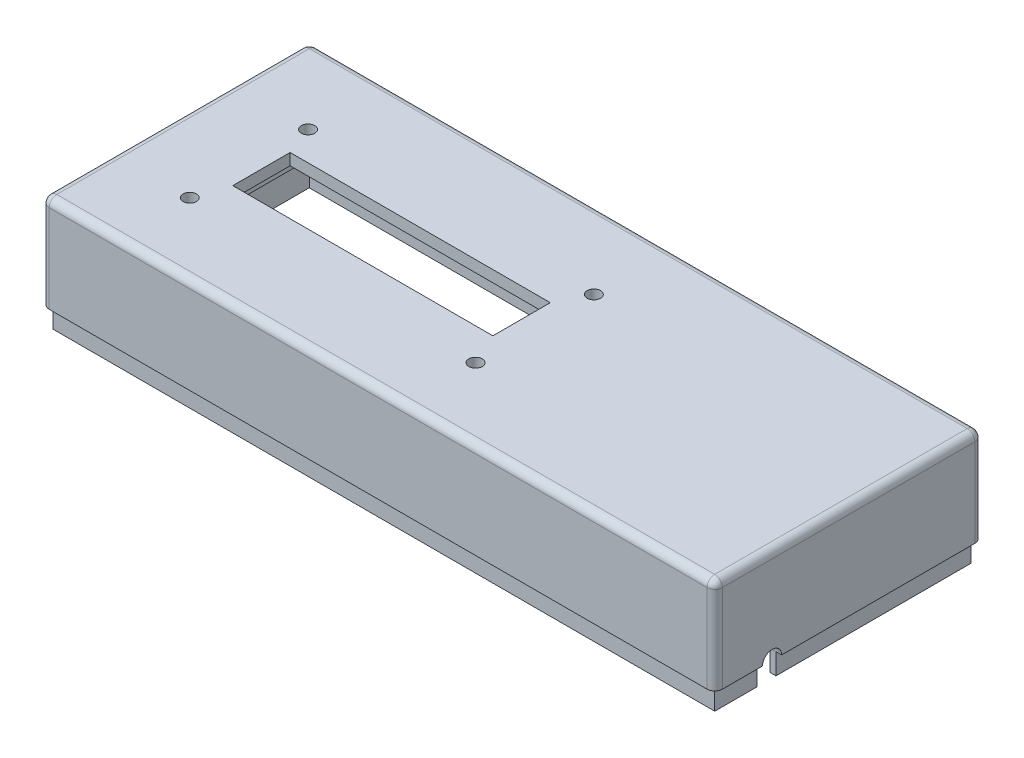
SolidWorks part; units mm, degrees
ref_plane "Front Plane" through (0, 0, 0) normal (0, 0, 1) x (1, 0, 0)
ref_plane "Top Plane" through (0, 0, 0) normal (0, 1, 0) x (1, 0, 0)
ref_plane "Right Plane" through (0, 0, 0) normal (1, 0, 0) x (0, 0, -1)
sketch "Sketch1" plane through (0, 0, 0) normal (0, 1, 0) x (1, 0, 0)
  line L1 (88, -35) -> (-88, -35)
  line L2 (88, -35) -> (88, 35)
  line L3 (88, 35) -> (-88, 35)
  line L4 (-88, -35) -> (-88, 35)
  line L5 (88, -35) -> (-88, 35) construction
  line L6 (88, 35) -> (-88, -35) construction
  point P0 (0, 0)
  dimension "D1" = 176
  dimension "D2" = 70
extrude "Boss-Extrude1" add sketch "Sketch1" along normal blind 30.5
sketch "Sketch2" plane through (0, 0, 0) normal (0, -1, 0) x (1, 0, 0)
  line L0 (-88, -35) -> (-88, 35) construction
  line L1 (85, -32) -> (-85, -32)
  line L2 (85, -32) -> (85, 32)
  line L3 (85, 32) -> (-85, 32)
  line L4 (-85, -32) -> (-85, 32)
  line L5 (85, -32) -> (-85, 32) construction
  line L6 (85, 32) -> (-85, -32) construction
  line L7 (88, -35) -> (-88, -35) construction
  line L9 (86.5, -33.5) -> (-86.5, -33.5)
  line L10 (86.5, -33.5) -> (86.5, 33.5)
  line L11 (86.5, 33.5) -> (-86.5, 33.5)
  line L12 (-86.5, -33.5) -> (-86.5, 33.5)
  line L13 (86.5, -33.5) -> (-86.5, 33.5) construction
  line L14 (86.5, 33.5) -> (-86.5, -33.5) construction
  line L15 (-88, 35) -> (88, 35)
  line L16 (-88, 35) -> (-88, -35)
  line L17 (-88, -35) -> (88, -35)
  line L18 (88, 35) -> (88, -35)
  point P0 (0, 0)
  point P10 (0, 0)
  dimension "D1" = 3
  dimension "D2" = 3
  dimension "D3" = 1.5
  dimension "D4" = 1.5
extrude "Cut-Extrude1" cut sketch "Sketch2" against normal blind 27.5 contours L4 L1 L2 L3
sketch "Sketch3" plane through (0, 0, 0) normal (0, -1, 0) x (1, 0, 0)
  line L1 (-86.5, 33.5) -> (86.5, 33.5)
  line L2 (-86.5, 33.5) -> (-86.5, -33.5)
  line L3 (-86.5, -33.5) -> (86.5, -33.5)
  line L4 (86.5, 33.5) -> (86.5, -33.5)
  line L5 (-88, 35) -> (88, 35)
  line L6 (-88, 35) -> (-88, -35)
  line L7 (-88, -35) -> (88, -35)
  line L8 (88, 35) -> (88, -35)
extrude "Cut-Extrude2" cut sketch "Sketch3" against normal blind 5.5
fillet "Fillet1" radius 2 8 edges at (-88, 30.5, 0) (0, 30.5, -35) (88, 30.5, 0) (0, 30.5, 35) (88, 18, 35) (88, 18, -35) (-88, 18, -35) (-88, 18, 35)
sketch "Sketch4" plane through (0, 27.5, 0) normal (0, -1, 0) x (1, 0, 0)
  line L0 (85, -32) -> (-85, -32) construction
  line L1 (-67, 13) -> (5, 13)
  line L2 (-67, 13) -> (-67, -12)
  line L3 (-67, -12) -> (5, -12)
  line L4 (5, 13) -> (5, -12)
  line L5 (-70, 16) -> (8, 16)
  line L6 (-70, 16) -> (-70, -15)
  line L7 (-70, -15) -> (8, -15)
  line L8 (8, 16) -> (8, -15)
  line L9 (-85, -32) -> (-85, 32) construction
  dimension "D1" = 25
  dimension "D2" = 72
  dimension "D3" = 20
  dimension "D4" = 3
  dimension "D5" = 15
  dimension "D6" = 3
  dimension "D7" = 3
  dimension "D8" = 3
extrude "Boss-Extrude2" add sketch "Sketch4" along normal blind 3
sketch "Sketch5" plane through (0, 27.5, 0) normal (0, -1, 0) x (1, 0, 0)
  line L0 (5, 13) -> (-67, 13) construction
  line L1 (-65, 8) -> (3, 8)
  line L2 (-65, 8) -> (-65, -7)
  line L3 (-65, -7) -> (3, -7)
  line L4 (3, 8) -> (3, -7)
  line L5 (-67, -12) -> (5, -12) construction
  line L6 (-67, 13) -> (-67, -12) construction
  line L7 (5, -12) -> (5, 13) construction
  dimension "D1" = 5
  dimension "D2" = 5
  dimension "D3" = 2
  dimension "D4" = 2
extrude "Cut-Extrude3" cut sketch "Sketch5" against normal up to next
sketch "Sketch6" plane through (0, 30.5, 0) normal (0, 1, 0) x (1, 0, 0)
  line L0 (3, 7) -> (3, -8) construction
  line L1 (-65, 7) -> (3, 7) construction
  circle A0 centre (-67.88, 14.57) radius 1.75
  circle A1 centre (6.83, 14.57) radius 1.75
  circle A2 centre (6.83, -16.36) radius 1.75
  circle A3 centre (-67.88, -16.36) radius 1.75
  dimension "D2" = 3.5
  dimension "D1" = 30.93
  dimension "D3" = 74.71
  dimension "D4" = 3.83
  dimension "D5" = 7.57
extrude "Cut-Extrude4" cut sketch "Sketch6" against normal up to next
sketch "Sketch8" plane through (88, 0, 0) normal (1, 0, 0) x (0, 0, -1)
  line L0 (33.5, 5.5) -> (-33.5, 5.5) construction
  line L1 (-35, 5.5) -> (-35, 28.5) construction
  line L2 (-22.5, 5.5) -> (-22.5, 0)
  line L3 (33.5, 0) -> (-33.5, 0) construction
  line L4 (-17.5, 5.5) -> (-17.5, 0)
  line L5 (-17.5, 0) -> (-22.5, 0)
  arc A0 (-17.5, 5.5) -> (-22.5, 5.5) centre (-20, 5.5) ccw
  dimension "D1" = 5
  dimension "D2" = 15
extrude "Cut-Extrude6" cut sketch "Sketch8" against normal up to next
